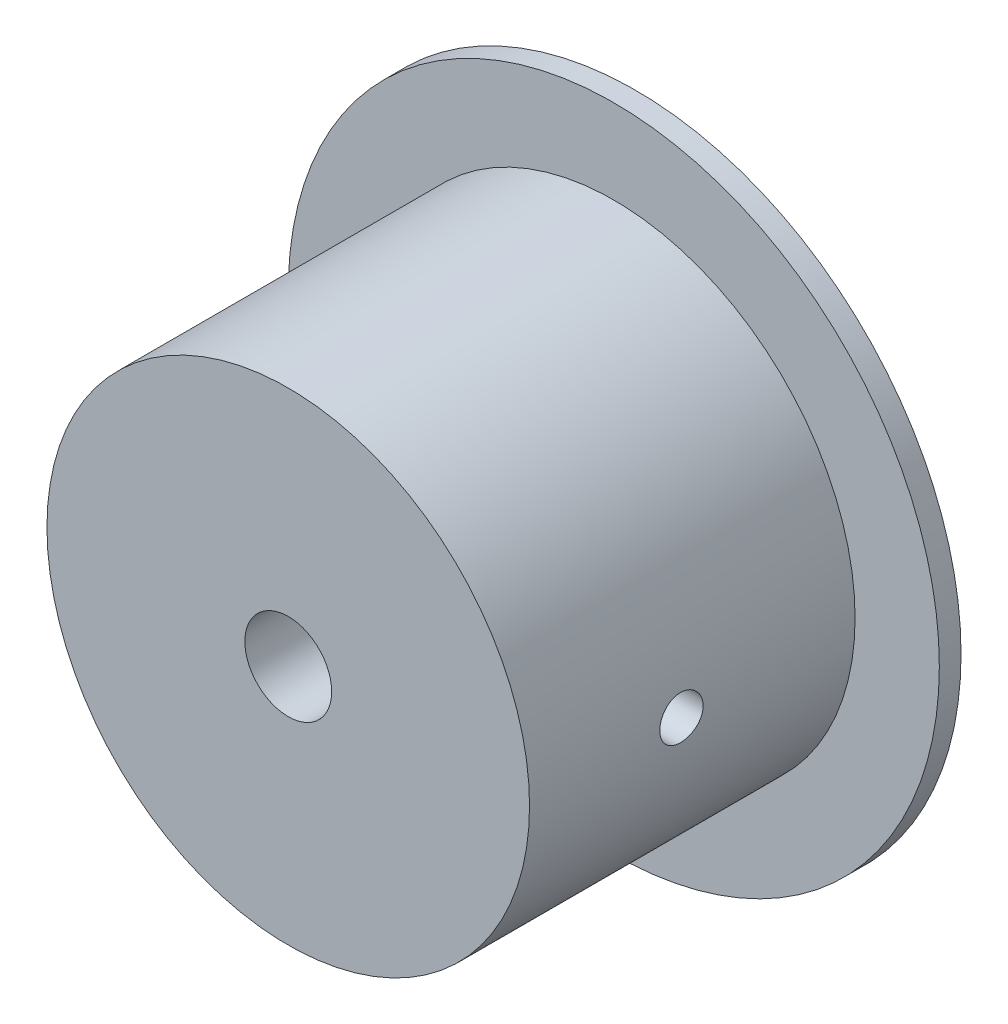
SolidWorks part; units mm, degrees
ref_plane "Ön Düzlem" through (0, 0, 0) normal (0, 0, 1) x (1, 0, 0)
ref_plane "Üst Düzlem" through (0, 0, 0) normal (0, 1, 0) x (1, 0, 0)
ref_plane "Sağ Düzlem" through (0, 0, 0) normal (1, 0, 0) x (0, 0, -1)
sketch "Çizim1" plane through (0, 0, 0) normal (0, 0, 1) x (1, 0, 0)
  circle A0 centre (-15.7997, 0) radius 15
  dimension "D1" = 30
extrude "Yükseklik-Ekstrüzyon1" add sketch "Çizim1" along normal blind 1
sketch "Çizim2" plane through (0, 0, 1) normal (0, 0, 1) x (1, 0, 0)
  circle A0 centre (-15.7997, 0) radius 11.118
extrude "Yükseklik-Ekstrüzyon2" add sketch "Çizim2" along normal blind 15
sketch "Çizim3" plane through (0, 0, 16) normal (0, 0, 1) x (1, 0, 0)
  circle A0 centre (-15.7997, 0) radius 2
  dimension "D1" = 4
extrude "Kes-Ekstrüzyon1" cut sketch "Çizim3" against normal through all
sketch "Sketch1" plane through (0, 0, 0) normal (1, 0, 0) x (0, 0, -1)
  line L0 (-16, 0) -> (0, 0) construction
  line L1 (-16, 11.118) -> (-16, -11.118) construction
  line L2 (-1, 15) -> (-1, -15) construction
  circle A0 centre (-9, 0) radius 1
  dimension "D1" = 2
  dimension "D2" = 8
extrude "Cut-Extrude1" cut sketch "Sketch1" against normal through all
